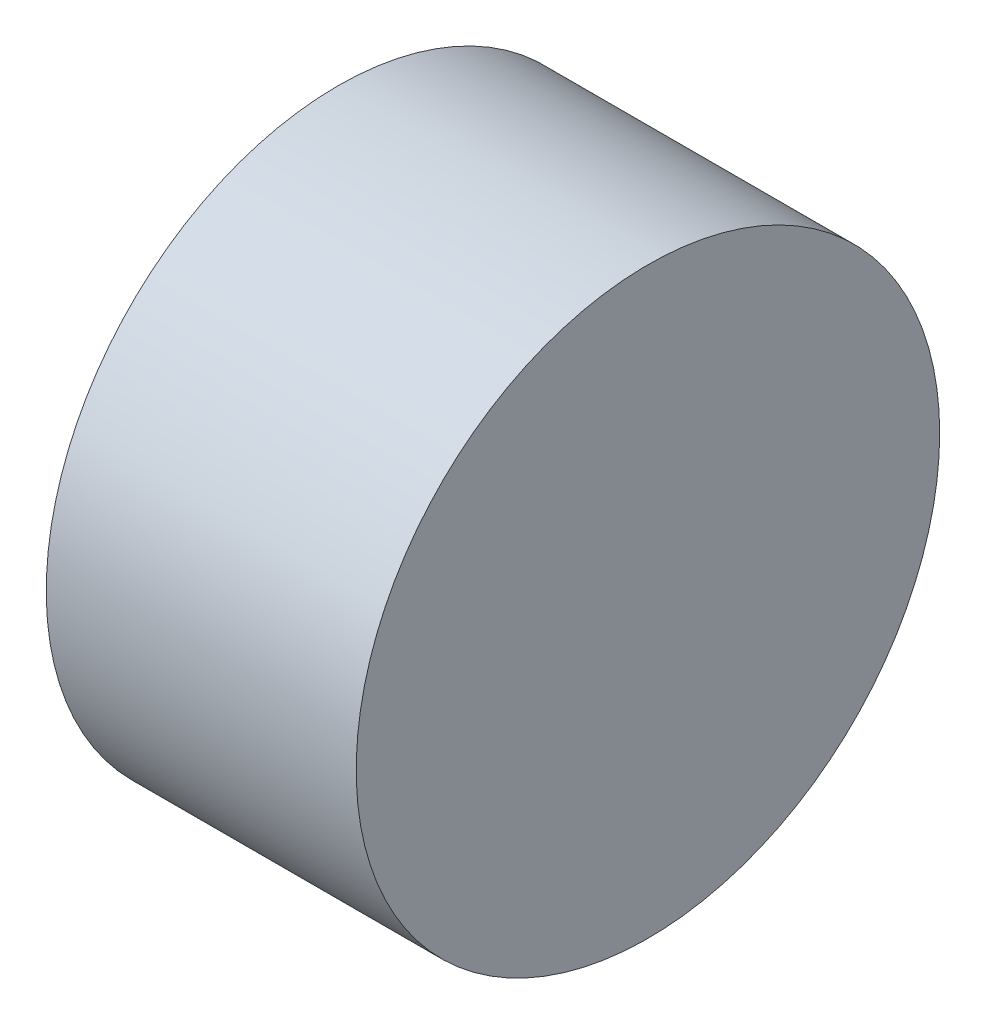
SolidWorks part; units mm, degrees
ref_plane "Front Plane" through (0, 0, 0) normal (0, 0, 1) x (1, 0, 0)
ref_plane "Top Plane" through (0, 0, 0) normal (0, 1, 0) x (1, 0, 0)
ref_plane "Right Plane" through (0, 0, 0) normal (1, 0, 0) x (0, 0, -1)
sketch "Sketch1" plane through (0, 0, 0) normal (1, 0, 0) x (0, 0, -1)
  line L0 (-1.5274, -2.157) -> (1.5274, -2.157) construction
  line L1 (-1.5274, -2.157) -> (1.5274, -2.157)
  circle A0 centre (0, 0) radius 4 construction
  circle A1 centre (0, 0) radius 4
  arc A2 (1.5274, -2.157) -> (-1.5274, -2.157) centre (0, 0) ccw construction
  arc A3 (1.5274, -2.157) -> (-1.5274, -2.157) centre (0, 0) ccw
extrude "Boss-Extrude1" add sketch "Sketch1" against normal offset from surface (3.25 mm away) 0.25
sketch "Sketch2" plane through (0, 0, 0) normal (1, 0, 0) x (0, 0, -1)
  circle A1 centre (0, 0) radius 4
  circle A2 centre (0, 0) radius 4
  dimension "D1" = 0
extrude "Boss-Extrude2" add sketch "Sketch2" along normal blind 1
